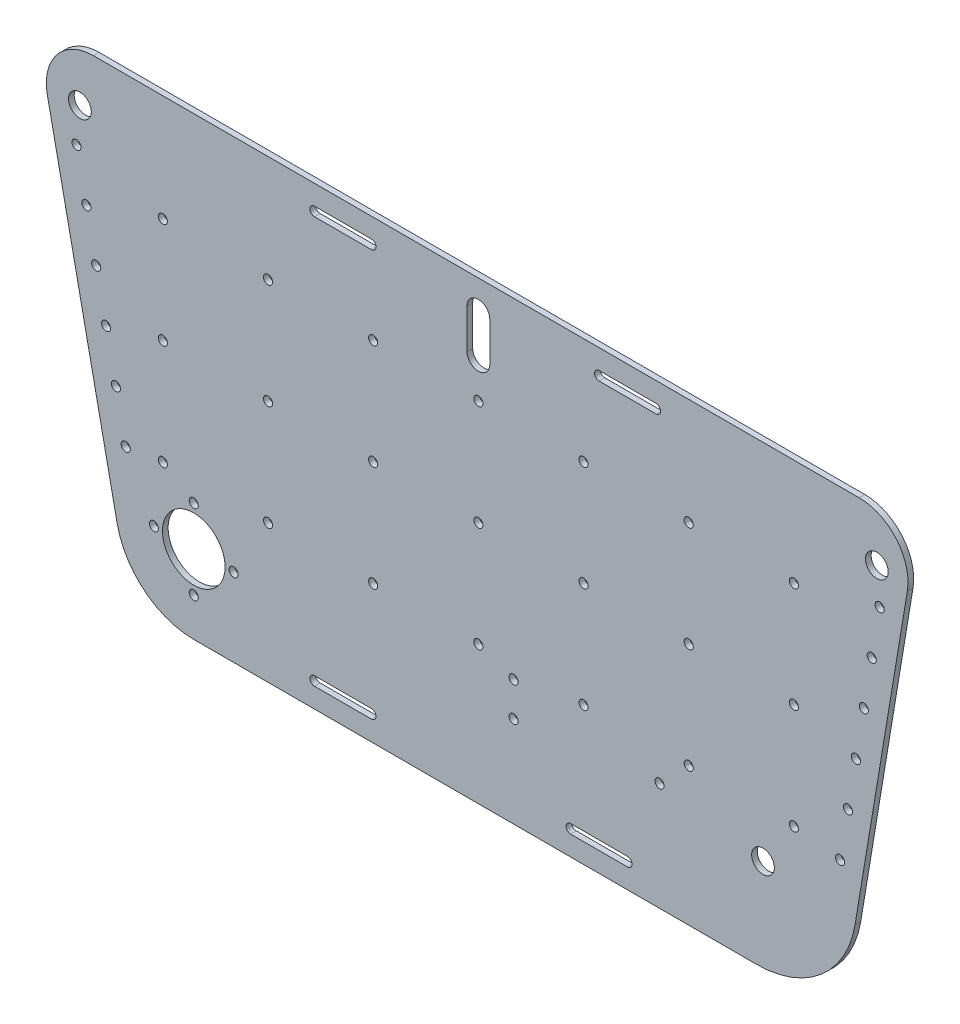
SolidWorks part; units mm, degrees
material "3.0205 (EN-AW 1200)"
ref_plane "Front Plane" through (0, 0, 0) normal (0, 0, 1) x (1, 0, 0)
ref_plane "Top Plane" through (0, 0, 0) normal (0, 1, 0) x (1, 0, 0)
ref_plane "Right Plane" through (0, 0, 0) normal (1, 0, 0) x (0, 0, -1)
sketch "Sketch1" plane through (0, 0, 0) normal (0, 0, 1) x (1, 0, 0)
  line L1 (0, 0) -> (0, 115.062) construction
  line L2 (-140, 115.062) -> (140, 115.062) construction
  line L3 (-100, -37.4683) -> (100, -37.4683)
  line L4 (142.2945, 0.8576) -> (153.4347, 113.7361)
  line L5 (137.3964, 128.3085) -> (2.6036, 101.8154)
  line L6 (-2.6036, 101.8154) -> (-137.3964, 128.3085)
  line L7 (-153.3748, 113.2277) -> (-137.1523, -5.0634)
  line L8 (100, -34.9683) -> (-100, -34.9683) construction
  arc A12 (-137.1523, -5.0634) -> (-100, -37.4683) centre (-100, 0.0317) ccw
  arc A13 (100, -37.4683) -> (142.2945, 0.8576) centre (100, 5.0317) ccw
  arc A14 (153.4347, 113.7361) -> (137.3964, 128.3085) centre (140, 115.062) ccw
  arc A15 (2.6036, 101.8154) -> (-2.6036, 101.8154) centre (0, 115.062) cw
  arc A16 (-137.3964, 128.3085) -> (-153.3748, 113.2277) centre (-140, 115.062) ccw
  point P8 (0, 115.062)
  point P26 (0, -34.9683)
  circle B0 centre (-100, 0.0317) radius 35
  circle B1 centre (100, 5.0317) radius 40
  circle B2 centre (-140, 115.062) radius 11
  circle B3 centre (0, 115.062) radius 11
  circle B4 centre (140, 115.062) radius 11
  dimension "D1" = 200
  dimension "D3" = 280
  dimension "D7" = 279.5095
  dimension "D8" = 165.7768
sketch_block_instance "Block2-1"
sketch_block "Block2" parameters "D1"=52.784
sketch_block_instance "Block3-1"
sketch_block "Block3" parameters "D1"=49.6633
sketch_block_instance "Block4-1"
sketch_block "Block4"
sketch_block_instance "Block5-1"
sketch_block "Block5" parameters "D1"=22
sketch_block_instance "Block6-1"
sketch_block "Block6"
other "Belt1"
sketch "Sketch5" plane through (0, 0, 0) normal (0, 0, 1) x (1, 0, 0)
  line L12 (-100, -37.4683) -> (100, -37.4683) construction
  line L25 (110.1118, -2.4683) -> (77.5737, -2.4683)
  line L26 (65.3235, -2.4683) -> (34.5589, -2.4683)
  line L27 (134.4186, -22.4683) -> (143.6762, -22.4683)
  line L28 (143.4347, -2.4683) -> (134.6111, -2.4683)
  line L29 (143.4347, -2.4683) -> (143.4347, -22.4683)
  line L30 (16.6763, -22.4683) -> (134.2763, -22.4683)
  line L31 (15.513, -2.4683) -> (7.5179, -2.4683)
  line L32 (15.513, -22.4683) -> (7.5179, -22.4683)
  line L33 (7.5179, -2.4683) -> (7.5179, -22.4683)
  line L57 (14.6295, 0.5317) -> (66.6561, 0.5317)
  line L58 (66.6561, 0.5317) -> (66.6561, 7.0446)
  line L59 (66.6561, 14.0189) -> (66.6561, 20.5317)
  line L60 (66.6561, 20.5317) -> (14.6295, 20.5317)
  line L61 (10.0864, 20.5317) -> (8.6561, 20.5317)
  line L62 (8.6561, 20.5317) -> (8.6561, 19.2625)
  line L63 (8.6561, 13.801) -> (8.6561, 7.2625)
  line L64 (8.6561, 1.801) -> (8.6561, 0.5317)
  line L65 (8.6561, 0.5317) -> (10.0864, 0.5317)
  circle A0 centre (100, 5.0317) radius 11
  circle A2 centre (100, 5.0317) radius 7
  circle A29 centre (63.6561, 10.5317) radius 1.6
  circle A30 centre (12.3579, 16.5317) radius 1.6
  arc A36 (66.6561, 7.0446) -> (66.6561, 14.0189) centre (63.6561, 10.5317) ccw
  arc A37 (14.6295, 20.5317) -> (10.0864, 20.5317) centre (12.3579, 16.5317) ccw
  arc A38 (8.6561, 19.2625) -> (8.6561, 13.801) centre (12.3579, 16.5317) ccw
  arc A39 (8.6561, 7.2625) -> (8.6561, 1.801) centre (12.3579, 4.5317) ccw
  arc A40 (10.0864, 0.5317) -> (14.6295, 0.5317) centre (12.3579, 4.5317) ccw
  circle A41 centre (12.3579, 4.5317) radius 1.6
  dimension "D1" = 3.2
  dimension "D2" = 4.6
  dimension "D23" = 22
  dimension "D24" = 14
  dimension "D3" = 1.1383
  dimension "D4" = 2.5685
  dimension "D5" = 4.8401
  dimension "D6" = 136.1584
  dimension "D7" = 7.9951
  dimension "D8" = 9.1584
  dimension "D9" = 27.0411
  dimension "D10" = 56.1383
  dimension "D11" = 57.8057
  dimension "D12" = 59.1383
  dimension "D13" = 70.0559
  dimension "D14" = 102.594
  dimension "D15" = 126.7584
  dimension "D16" = 126.9007
  dimension "D17" = 127.0932
  dimension "D18" = 135.9169
  dimension "D19" = 20
  dimension "D20" = 23
  dimension "D21" = 29.5129
  dimension "D22" = 15
  dimension "D25" = 10
sketch "Sketch3" plane through (0, 0, 0) normal (0, 0, 1) x (1, 0, 0)
  line L0 (-100, -27.4683) -> (97.7714, -27.4683)
  line L1 (-100, -37.4683) -> (100, -37.4683) construction
  line L2 (-126.9257, -5.5588) -> (-151.4564, 112.5875)
  line L3 (132.3429, 1.8398) -> (150.7181, 112.5875)
  line L4 (-137.1523, -5.0634) -> (-126.9257, -5.5588) construction
  line L6 (142.2945, 0.8576) -> (132.3429, 1.8398) construction
  line L7 (142.2945, 0.8576) -> (153.4347, 113.7361) construction
  line L8 (-135.2278, 132.5317) -> (133.8103, 132.5317)
  line L9 (-4, 121.9902) -> (-4, 108.1338)
  line L10 (4, 121.9902) -> (4, 108.1338)
  circle A0 centre (-140, 115.062) radius 4
  circle A1 centre (0, 115.062) radius 4
  circle A2 centre (140, 115.062) radius 4
  circle A3 centre (100, 5.0317) radius 4
  circle A4 centre (-100, 0.0317) radius 11
  circle A6 centre (140, 115.062) radius 11 construction
  arc A7 (-100, -27.4683) -> (-126.9257, -5.5588) centre (-100, 0.0317) cw
  arc A8 (97.7714, -27.4683) -> (132.3429, 1.8398) centre (97.7714, 7.5758) ccw
  arc A10 (-151.4564, 112.5875) -> (-135.2278, 132.5317) centre (-135.2278, 115.9571) cw
  arc A11 (150.7181, 112.5875) -> (133.8103, 132.5317) centre (133.8103, 115.3929) ccw
  circle A13 centre (63.6561, 10.5317) radius 1.6 construction
  circle A14 centre (12.3579, 4.5317) radius 1.6 construction
  circle A15 centre (12.3579, 16.5317) radius 1.6 construction
  circle A16 centre (63.6561, 10.5317) radius 1.6
  circle A17 centre (12.3579, 4.5317) radius 1.6
  circle A18 centre (12.3579, 16.5317) radius 1.6
  circle A19 centre (-100, 0.0317) radius 14 construction
  circle A20 centre (-100, 14.0317) radius 1.6
  circle A21 centre (-86, 0.0317) radius 1.6
  circle A22 centre (-100, -13.9683) radius 1.6
  circle A23 centre (-114, 0.0317) radius 1.6
  circle A24 centre (0, 115.062) radius 8 construction
  arc A25 (-4, 121.9902) -> (4, 121.9902) centre (0, 121.9902) cw
  arc A26 (-4, 108.1338) -> (4, 108.1338) centre (0, 108.1338) ccw
  dimension "D1" = 8
  dimension "D5" = 22
  dimension "D6" = 28
  dimension "D7" = 3.2
  dimension "D2" = 10
  dimension "D3" = 10
  dimension "D4" = 160
  dimension "D9" = 8
  dimension "D8" = 4
extrude "Boss-Extrude1" add sketch "Sketch3" along normal blind 2 contours A10 L2 A7 L0 A8 L3 A11 L8 A26 L9 A25 L10 A23 A22 A21 A20 A18 A17 A16 A4 A3 A2 A0
sketch "Sketch6" plane through (0, 0, 0) normal (0, 0, 1) x (1, 0, 0)
  line L0 (-57.58, -17.2983) -> (-37.58, -17.2983)
  line L1 (-57.58, -20.4983) -> (-37.58, -20.4983)
  line L2 (32.42, -17.2983) -> (52.42, -17.2983)
  line L3 (32.42, -20.4983) -> (52.42, -20.4983)
  line L4 (-100, -27.4683) -> (97.7714, -27.4683) construction
  line L5 (32.42, -18.8983) -> (-37.58, -18.8983) construction
  line L6 (-25.08, -27.4683) -> (-25.08, 132.5317) construction
  line L7 (-135.2278, 132.5317) -> (133.8103, 132.5317) construction
  line L8 (-25.08, 52.5317) -> (-5.468, 52.5317) construction
  line L9 (-57.58, 125.5617) -> (-37.58, 125.5617)
  line L10 (-57.58, 122.3617) -> (-37.58, 122.3617)
  line L11 (42.42, 125.5617) -> (62.42, 125.5617)
  line L12 (42.42, 122.3617) -> (62.42, 122.3617)
  arc A0 (-57.58, -17.2983) -> (-57.58, -20.4983) centre (-57.58, -18.8983) ccw
  arc A1 (-37.58, -17.2983) -> (-37.58, -20.4983) centre (-37.58, -18.8983) cw
  arc A2 (52.42, -17.2983) -> (52.42, -20.4983) centre (52.42, -18.8983) cw
  arc A3 (32.42, -17.2983) -> (32.42, -20.4983) centre (32.42, -18.8983) ccw
  arc A4 (-37.58, 122.3617) -> (-37.58, 125.5617) centre (-37.58, 123.9617) ccw
  arc A5 (-57.58, 122.3617) -> (-57.58, 125.5617) centre (-57.58, 123.9617) cw
  arc A6 (42.42, 122.3617) -> (42.42, 125.5617) centre (42.42, 123.9617) cw
  arc A7 (62.42, 122.3617) -> (62.42, 125.5617) centre (62.42, 123.9617) ccw
  point P6 (-47.58, -17.2983)
  dimension "D1" = 3.2
  dimension "D2" = 52.42
  dimension "D3" = 20
  dimension "D5" = 8.57
  dimension "D6" = 2
  dimension "D7" = 70
  dimension "D4" = 2
extrude "Cut-Extrude3" cut sketch "Sketch6" along normal through all
ref_plane "Plane1" through (0, 52.5317, 0) normal (0, -1, 0) x (-1, 0, 0)
sketch "Sketch7" plane through (0, 0, 2) normal (0, 0, 1) x (1, 0, 0)
  line L0 (0, 95.0743) -> (0, 104.1338) construction
  line L1 (-88.8055, 84.3587) -> (-73.8055, 84.3587) construction
  line L2 (-88.8055, 84.3587) -> (-88.8055, 69.3587) construction
  line L3 (-88.8055, 69.3587) -> (-73.8055, 69.3587) construction
  line L4 (-73.8055, 84.3587) -> (-73.8055, 69.3587) construction
  line L5 (-88.8055, 84.3587) -> (-73.8055, 69.3587) construction
  line L6 (-88.8055, 69.3587) -> (-73.8055, 84.3587) construction
  line L7 (-141.1844, 102.4668) -> (-121.897, 9.5732) construction
  line L8 (-126.9257, -5.5588) -> (-151.4564, 112.5875) construction
  line L9 (-1.1, 52.5317) -> (1.1, 52.5317) construction
  line L10 (140.9921, 102.8439) -> (122.5363, -8.3891) construction
  line L12 (132.3429, 1.8398) -> (150.7181, 112.5875) construction
  circle A0 centre (-110.8622, 95.0743) radius 1.6
  circle A1 centre (-73.9081, 95.0743) radius 1.6
  circle A2 centre (-36.9541, 95.0743) radius 1.6
  circle A3 centre (0, 95.0743) radius 1.6
  circle A4 centre (36.9541, 95.0743) radius 1.6
  circle A5 centre (73.9081, 95.0743) radius 1.6
  circle A6 centre (110.8622, 95.0743) radius 1.6
  circle A7 centre (-73.9081, 58.0743) radius 1.6
  circle A8 centre (-36.9541, 58.0743) radius 1.6
  circle A9 centre (0, 58.0743) radius 1.6
  circle A10 centre (36.9541, 58.0743) radius 1.6
  circle A11 centre (73.9081, 58.0743) radius 1.6
  circle A12 centre (110.8622, 58.0743) radius 1.6
  circle A13 centre (-73.9081, 21.0743) radius 1.6
  circle A14 centre (-36.9541, 21.0743) radius 1.6
  circle A15 centre (0, 21.0743) radius 1.6
  circle A16 centre (36.9541, 21.0743) radius 1.6
  circle A17 centre (73.9081, 21.0743) radius 1.6
  circle A18 centre (110.8622, 21.0743) radius 1.6
  circle A19 centre (-110.8622, 58.0743) radius 1.6
  circle A20 centre (-110.8622, 21.0743) radius 1.6
  arc A21 (-4, 108.1338) -> (4, 108.1338) centre (0, 108.1338) ccw construction
  circle A22 centre (-141.1844, 102.4668) radius 1.6
  circle A23 centre (-137.7284, 85.8218) radius 1.6
  circle A24 centre (-134.2724, 69.1767) radius 1.6
  circle A25 centre (-130.8164, 52.5317) radius 1.6
  circle A26 centre (-127.3604, 35.8867) radius 1.6
  circle A27 centre (-123.9044, 19.2417) radius 1.6
  circle A28 centre (140.9921, 102.8439) radius 1.6
  circle A29 centre (138.2095, 86.0732) radius 1.6
  circle A30 centre (135.4269, 69.3025) radius 1.6
  circle A31 centre (132.6443, 52.5317) radius 1.6
  circle A32 centre (129.8617, 35.761) radius 1.6
  circle A33 centre (127.0791, 18.9903) radius 1.6
  point P0 (-81.3055, 76.8587)
  dimension "D1" = 3.2
  dimension "D4" = 6
  dimension "D6" = 8
  dimension "D2" = 7
  dimension "D5" = 8
  dimension "D3" = 3
  dimension "D7" = 6
extrude "Cut-Extrude4" cut sketch "Sketch7" against normal through all
